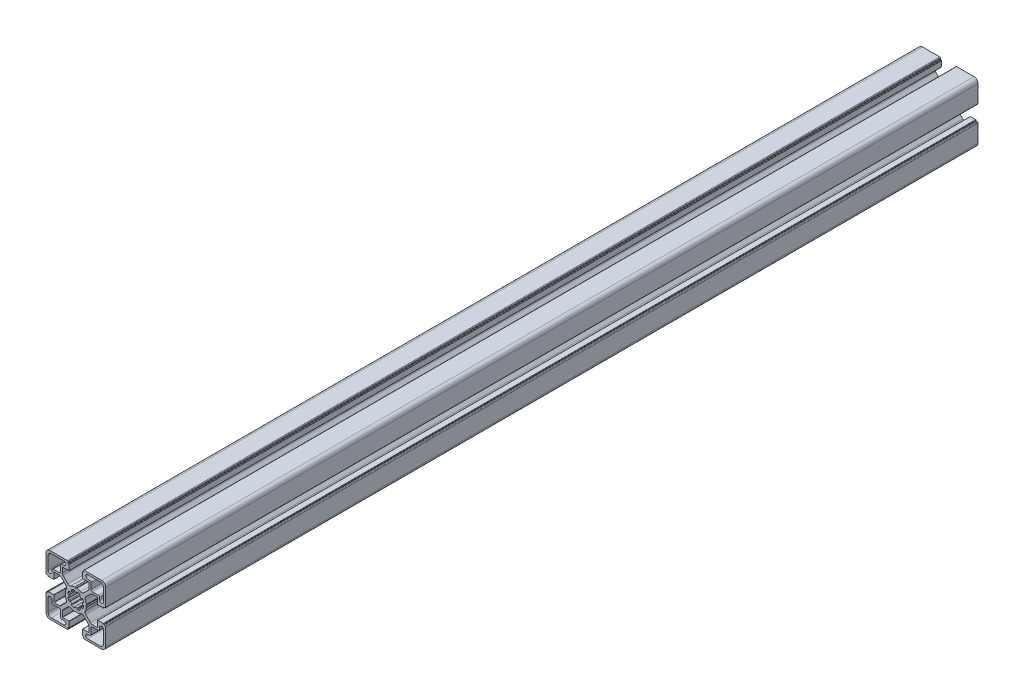
SolidWorks part; units mm, degrees
ref_plane "Front Plane" through (0, 0, 0) normal (0, 0, 1) x (1, 0, 0)
ref_plane "Top Plane" through (0, 0, 0) normal (0, 1, 0) x (1, 0, 0)
ref_plane "Right Plane" through (0, 0, 0) normal (1, 0, 0) x (0, 0, -1)
sketch "Sketch1" plane through (0, 0, 0) normal (0, 0, 1) x (1, 0, 0)
  line L0 (10.55, 18) -> (9, 18)
  line L1 (18.5, 21) -> (9, 21)
  line L2 (21, 9.0002) -> (21, 18.5)
  line L3 (18, 9.0002) -> (18, 10.55)
  line L4 (17, 11.55) -> (12.55, 11.55)
  line L5 (11.55, 12.55) -> (11.55, 17)
  line L6 (7.974, 0.7926) -> (7.5401, 0.0468)
  line L7 (-0.8674, 4.9242) -> (-0.9675, 5.4811)
  line L8 (-3.1913, 4.5626) -> (-2.864, 4.0985)
  line L9 (-4.0897, 2.8765) -> (-4.5668, 3.2082)
  line L10 (-5.4897, 0.9862) -> (-4.9205, 0.8878)
  line L11 (11.1298, 9.425) -> (7.5635, 5.8587)
  line L12 (16.3169, 9.9945) -> (12.5048, 9.9945)
  line L13 (16.5169, 5.2) -> (16.5169, 9.7945)
  line L14 (20.7196, 5) -> (16.7169, 5)
  line L15 (21.0196, 5.3) -> (21.0196, 5.5)
  line L16 (22, 5.8) -> (21.3196, 5.8)
  line L17 (22.5, 6.3) -> (22.5, 19.5)
  line L18 (19.5, 22.5) -> (6.3757, 22.5)
  line L19 (5.8757, 21.3) -> (5.8757, 22)
  line L20 (5.5757, 21) -> (5.3, 21)
  line L21 (5, 16.6668) -> (5, 20.7)
  line L22 (9.9054, 16.4668) -> (5.2, 16.4668)
  line L23 (10.1054, 12.4716) -> (10.1054, 16.2668)
  line L24 (5.9449, 7.4827) -> (9.5196, 11.0574)
  line L25 (0.1126, 7.6069) -> (0.7547, 7.9748)
  line L26 (5.4897, 0.9862) -> (4.9205, 0.8878)
  line L27 (4.0897, 2.8765) -> (4.5668, 3.2082)
  line L28 (3.1913, 4.5626) -> (2.864, 4.0985)
  line L29 (0.8674, 4.9242) -> (0.9675, 5.4811)
  line L30 (-10.55, -18) -> (-9, -18)
  line L31 (-18.5, -21) -> (-9, -21)
  line L32 (-21, -9.0002) -> (-21, -18.5)
  line L33 (-18, -9.0002) -> (-18, -10.55)
  line L34 (-17, -11.55) -> (-12.55, -11.55)
  line L35 (-11.55, -12.55) -> (-11.55, -17)
  line L36 (-7.974, -0.7926) -> (-7.5401, -0.0468)
  line L37 (-11.1298, -9.425) -> (-7.5635, -5.8587)
  line L38 (-16.3169, -9.9945) -> (-12.5048, -9.9945)
  line L39 (-16.5169, -5.2) -> (-16.5169, -9.7945)
  line L40 (-20.7196, -5) -> (-16.7169, -5)
  line L41 (-21.0196, -5.3) -> (-21.0196, -5.5)
  line L42 (-22, -5.8) -> (-21.3196, -5.8)
  line L43 (-22.5, -6.3) -> (-22.5, -19.5)
  line L44 (-19.5, -22.5) -> (-6.3757, -22.5)
  line L45 (-5.8757, -21.3) -> (-5.8757, -22)
  line L46 (-5.5757, -21) -> (-5.3, -21)
  line L47 (-5, -16.6668) -> (-5, -20.7)
  line L48 (-9.9054, -16.4668) -> (-5.2, -16.4668)
  line L49 (-10.1054, -12.4716) -> (-10.1054, -16.2668)
  line L50 (-5.9449, -7.4827) -> (-9.5196, -11.0574)
  line L51 (-0.1126, -7.6069) -> (-0.7547, -7.9748)
  line L52 (0.8674, -4.9242) -> (0.9675, -5.4811)
  line L53 (3.1913, -4.5626) -> (2.864, -4.0985)
  line L54 (4.0897, -2.8765) -> (4.5668, -3.2082)
  line L55 (5.4897, -0.9862) -> (4.9205, -0.8878)
  line L56 (0.1126, -7.6069) -> (0.7547, -7.9748)
  line L57 (5.9449, -7.4827) -> (9.5196, -11.0574)
  line L58 (10.1054, -12.4716) -> (10.1054, -16.2668)
  line L59 (9.9054, -16.4668) -> (5.2, -16.4668)
  line L60 (5, -16.6668) -> (5, -20.7)
  line L61 (5.5757, -21) -> (5.3, -21)
  line L62 (-0.1126, 7.6069) -> (-0.7547, 7.9748)
  line L63 (-5.9449, 7.4827) -> (-9.5196, 11.0574)
  line L64 (-10.1054, 12.4716) -> (-10.1054, 16.2668)
  line L65 (-9.9054, 16.4668) -> (-5.2, 16.4668)
  line L66 (-5, 16.6668) -> (-5, 20.7)
  line L67 (-5.5757, 21) -> (-5.3, 21)
  line L68 (-5.8757, 21.3) -> (-5.8757, 22)
  line L69 (-19.5, 22.5) -> (-6.3757, 22.5)
  line L70 (-22.5, 6.3) -> (-22.5, 19.5)
  line L71 (-22, 5.8) -> (-21.3196, 5.8)
  line L72 (-21.0196, 5.3) -> (-21.0196, 5.5)
  line L73 (-20.7196, 5) -> (-16.7169, 5)
  line L74 (-16.5169, 5.2) -> (-16.5169, 9.7945)
  line L75 (-16.3169, 9.9945) -> (-12.5048, 9.9945)
  line L76 (-11.1298, 9.425) -> (-7.5635, 5.8587)
  line L77 (-7.974, 0.7926) -> (-7.5401, 0.0468)
  line L78 (5.8757, -21.3) -> (5.8757, -22)
  line L79 (19.5, -22.5) -> (6.3757, -22.5)
  line L80 (22.5, -6.3) -> (22.5, -19.5)
  line L81 (22, -5.8) -> (21.3196, -5.8)
  line L82 (21.0196, -5.3) -> (21.0196, -5.5)
  line L83 (20.7196, -5) -> (16.7169, -5)
  line L84 (16.5169, -5.2) -> (16.5169, -9.7945)
  line L85 (16.3169, -9.9945) -> (12.5048, -9.9945)
  line L86 (11.1298, -9.425) -> (7.5635, -5.8587)
  line L87 (-5.4897, -0.9862) -> (-4.9205, -0.8878)
  line L88 (-4.0897, -2.8765) -> (-4.5668, -3.2082)
  line L89 (-3.1913, -4.5626) -> (-2.864, -4.0985)
  line L90 (-0.8674, -4.9242) -> (-0.9675, -5.4811)
  line L91 (7.974, -0.7926) -> (7.5401, -0.0468)
  line L92 (-11.55, 12.55) -> (-11.55, 17)
  line L93 (-17, 11.55) -> (-12.55, 11.55)
  line L94 (-18, 9.0002) -> (-18, 10.55)
  line L95 (-21, 9.0002) -> (-21, 18.5)
  line L96 (-18.5, 21) -> (-9, 21)
  line L97 (-10.55, 18) -> (-9, 18)
  line L98 (11.55, -12.55) -> (11.55, -17)
  line L99 (17, -11.55) -> (12.55, -11.55)
  line L100 (18, -9.0002) -> (18, -10.55)
  line L101 (21, -9.0002) -> (21, -18.5)
  line L102 (18.5, -21) -> (9, -21)
  line L103 (10.55, -18) -> (9, -18)
  line L104 (-33.3633, 0) -> (37.7265, 0) construction
  line L105 (0, 32.2957) -> (0, -36.0465) construction
  arc A0 (9, 18) -> (9, 21) centre (9, 19.5) cw
  arc A1 (18.5, 21) -> (21, 18.5) centre (18.5, 18.5) cw
  arc A2 (21, 9.0002) -> (18, 9.0002) centre (19.5, 9.0002) cw
  arc A3 (17, 11.55) -> (18, 10.55) centre (17, 10.55) cw
  arc A4 (12.55, 11.55) -> (11.55, 12.55) centre (12.55, 12.55) cw
  arc A5 (10.55, 18) -> (11.55, 17) centre (10.55, 17) cw
  arc A6 (7.5313, 0) -> (7.5401, 0.0468) centre (7.7309, -0.013) cw
  arc A7 (8, 0.9141) -> (7.974, 0.7926) centre (7.8011, 0.8932) cw
  arc A8 (7.2004, 3.6119) -> (8, 0.9141) centre (0.0496, 0.0249) cw
  arc A9 (7.2004, 3.6119) -> (7.5635, 5.8587) centre (8.9385, 4.4837) cw
  arc A10 (11.1298, 9.425) -> (12.5048, 9.9945) centre (12.5048, 8.05) cw
  arc A11 (16.3169, 9.9945) -> (16.5169, 9.7945) centre (16.3169, 9.7945) cw
  arc A12 (16.7169, 5) -> (16.5169, 5.2) centre (16.7169, 5.2) cw
  arc A13 (21.0196, 5.3) -> (20.7196, 5) centre (20.7196, 5.3) cw
  arc A14 (0.8674, 4.9242) -> (-0.8674, 4.9242) centre (0, 0) ccw
  arc A15 (-0.9675, 5.4811) -> (-1.5951, 5.8941) centre (-1.4627, 5.4119) ccw
  arc A16 (-1.5951, 5.8941) -> (-3.0444, 5.2994) centre (-0.0235, 0) ccw
  arc A17 (-3.0444, 5.2994) -> (-3.1913, 4.5626) centre (-2.7943, 4.8665) ccw
  arc A18 (-2.864, 4.0985) -> (-4.0897, 2.8765) centre (0, 0) ccw
  arc A19 (-4.5668, 3.2082) -> (-5.3025, 3.0565) centre (-4.868, 2.8091) ccw
  arc A20 (-5.3025, 3.0565) -> (-5.9068, 1.6112) centre (-0.0235, 0) ccw
  arc A21 (-5.9068, 1.6112) -> (-5.4897, 0.9862) centre (-5.4239, 1.4819) ccw
  arc A22 (-4.9205, 0.8878) -> (-5, 0) centre (0, 0) ccw
  arc A23 (21.0196, 5.5) -> (21.3196, 5.8) centre (21.3196, 5.5) cw
  arc A24 (22.5, 6.3) -> (22, 5.8) centre (22, 6.3) cw
  arc A25 (19.5, 22.5) -> (22.5, 19.5) centre (19.5, 19.5) cw
  arc A26 (5.8757, 22) -> (6.3757, 22.5) centre (6.3757, 22) cw
  arc A27 (5.8757, 21.3) -> (5.5757, 21) centre (5.5757, 21.3) cw
  arc A28 (5, 20.7) -> (5.3, 21) centre (5.3, 20.7) cw
  arc A29 (5.2, 16.4668) -> (5, 16.6668) centre (5.2, 16.6668) cw
  arc A30 (9.9054, 16.4668) -> (10.1054, 16.2668) centre (9.9054, 16.2668) cw
  arc A31 (10.1054, 12.4716) -> (9.5196, 11.0574) centre (8.1054, 12.4716) cw
  arc A32 (5.9449, 7.4827) -> (3.6665, 7.1733) centre (4.5855, 8.9496) cw
  arc A33 (0.8764, 8) -> (3.6665, 7.1733) centre (0.0235, 0) cw
  arc A34 (0.7547, 7.9748) -> (0.8764, 8) centre (0.8542, 7.8013) cw
  arc A35 (0.1126, 7.6069) -> (0, 7.531) centre (-0.0489, 7.7249) cw
  arc A36 (4.9205, 0.8878) -> (5, 0) centre (0, 0) cw
  arc A37 (5.9068, 1.6112) -> (5.4897, 0.9862) centre (5.4239, 1.4819) cw
  arc A38 (5.3025, 3.0565) -> (5.9068, 1.6112) centre (0.0235, 0) cw
  arc A39 (4.5668, 3.2082) -> (5.3025, 3.0565) centre (4.868, 2.8091) cw
  arc A40 (2.864, 4.0985) -> (4.0897, 2.8765) centre (0, 0) cw
  arc A41 (3.0444, 5.2994) -> (3.1913, 4.5626) centre (2.7943, 4.8665) cw
  arc A42 (1.5951, 5.8941) -> (3.0444, 5.2994) centre (0.0235, 0) cw
  arc A43 (0.9675, 5.4811) -> (1.5951, 5.8941) centre (1.4627, 5.4119) cw
  arc A44 (-9, -18) -> (-9, -21) centre (-9, -19.5) cw
  arc A45 (-18.5, -21) -> (-21, -18.5) centre (-18.5, -18.5) cw
  arc A46 (-21, -9.0002) -> (-18, -9.0002) centre (-19.5, -9.0002) cw
  arc A47 (-17, -11.55) -> (-18, -10.55) centre (-17, -10.55) cw
  arc A48 (-12.55, -11.55) -> (-11.55, -12.55) centre (-12.55, -12.55) cw
  arc A49 (-10.55, -18) -> (-11.55, -17) centre (-10.55, -17) cw
  arc A50 (-7.5313, 0) -> (-7.5401, -0.0468) centre (-7.7309, 0.013) cw
  arc A51 (-8, -0.9141) -> (-7.974, -0.7926) centre (-7.8011, -0.8932) cw
  arc A52 (-7.2004, -3.6119) -> (-8, -0.9141) centre (-0.0496, -0.0249) cw
  arc A53 (-7.2004, -3.6119) -> (-7.5635, -5.8587) centre (-8.9385, -4.4837) cw
  arc A54 (-11.1298, -9.425) -> (-12.5048, -9.9945) centre (-12.5048, -8.05) cw
  arc A55 (-16.3169, -9.9945) -> (-16.5169, -9.7945) centre (-16.3169, -9.7945) cw
  arc A56 (-16.7169, -5) -> (-16.5169, -5.2) centre (-16.7169, -5.2) cw
  arc A57 (-21.0196, -5.3) -> (-20.7196, -5) centre (-20.7196, -5.3) cw
  arc A58 (-21.0196, -5.5) -> (-21.3196, -5.8) centre (-21.3196, -5.5) cw
  arc A59 (-22.5, -6.3) -> (-22, -5.8) centre (-22, -6.3) cw
  arc A60 (-19.5, -22.5) -> (-22.5, -19.5) centre (-19.5, -19.5) cw
  arc A61 (-5.8757, -22) -> (-6.3757, -22.5) centre (-6.3757, -22) cw
  arc A62 (-5.8757, -21.3) -> (-5.5757, -21) centre (-5.5757, -21.3) cw
  arc A63 (-5, -20.7) -> (-5.3, -21) centre (-5.3, -20.7) cw
  arc A64 (-5.2, -16.4668) -> (-5, -16.6668) centre (-5.2, -16.6668) cw
  arc A65 (-9.9054, -16.4668) -> (-10.1054, -16.2668) centre (-9.9054, -16.2668) cw
  arc A66 (-10.1054, -12.4716) -> (-9.5196, -11.0574) centre (-8.1054, -12.4716) cw
  arc A67 (-5.9449, -7.4827) -> (-3.6665, -7.1733) centre (-4.5855, -8.9496) cw
  arc A68 (-0.8764, -8) -> (-3.6665, -7.1733) centre (-0.0235, 0) cw
  arc A69 (-0.7547, -7.9748) -> (-0.8764, -8) centre (-0.8542, -7.8013) cw
  arc A70 (-0.1126, -7.6069) -> (0, -7.531) centre (0.0489, -7.7249) cw
  arc A71 (0.9675, -5.4811) -> (1.5951, -5.8941) centre (1.4627, -5.4119) ccw
  arc A72 (1.5951, -5.8941) -> (3.0444, -5.2994) centre (0.0235, 0) ccw
  arc A73 (3.0444, -5.2994) -> (3.1913, -4.5626) centre (2.7943, -4.8665) ccw
  arc A74 (2.864, -4.0985) -> (4.0897, -2.8765) centre (0, 0) ccw
  arc A75 (4.5668, -3.2082) -> (5.3025, -3.0565) centre (4.868, -2.8091) ccw
  arc A76 (5.3025, -3.0565) -> (5.9068, -1.6112) centre (0.0235, 0) ccw
  arc A77 (5.9068, -1.6112) -> (5.4897, -0.9862) centre (5.4239, -1.4819) ccw
  arc A78 (4.9205, -0.8878) -> (5, 0) centre (0, 0) ccw
  arc A79 (0.1126, -7.6069) -> (0, -7.531) centre (-0.0489, -7.7249) ccw
  arc A80 (0.7547, -7.9748) -> (0.8764, -8) centre (0.8542, -7.8013) ccw
  arc A81 (0.8764, -8) -> (3.6665, -7.1733) centre (0.0235, 0) ccw
  arc A82 (5.9449, -7.4827) -> (3.6665, -7.1733) centre (4.5855, -8.9496) ccw
  arc A83 (10.1054, -12.4716) -> (9.5196, -11.0574) centre (8.1054, -12.4716) ccw
  arc A84 (9.9054, -16.4668) -> (10.1054, -16.2668) centre (9.9054, -16.2668) ccw
  arc A85 (5.2, -16.4668) -> (5, -16.6668) centre (5.2, -16.6668) ccw
  arc A86 (5, -20.7) -> (5.3, -21) centre (5.3, -20.7) ccw
  arc A87 (5.8757, -21.3) -> (5.5757, -21) centre (5.5757, -21.3) ccw
  arc A88 (-0.1126, 7.6069) -> (0, 7.531) centre (0.0489, 7.7249) ccw
  arc A89 (-0.7547, 7.9748) -> (-0.8764, 8) centre (-0.8542, 7.8013) ccw
  arc A90 (-0.8764, 8) -> (-3.6665, 7.1733) centre (-0.0235, 0) ccw
  arc A91 (-5.9449, 7.4827) -> (-3.6665, 7.1733) centre (-4.5855, 8.9496) ccw
  arc A92 (-10.1054, 12.4716) -> (-9.5196, 11.0574) centre (-8.1054, 12.4716) ccw
  arc A93 (-9.9054, 16.4668) -> (-10.1054, 16.2668) centre (-9.9054, 16.2668) ccw
  arc A94 (-5.2, 16.4668) -> (-5, 16.6668) centre (-5.2, 16.6668) ccw
  arc A95 (-5, 20.7) -> (-5.3, 21) centre (-5.3, 20.7) ccw
  arc A96 (-5.8757, 21.3) -> (-5.5757, 21) centre (-5.5757, 21.3) ccw
  arc A97 (-5.8757, 22) -> (-6.3757, 22.5) centre (-6.3757, 22) ccw
  arc A98 (-19.5, 22.5) -> (-22.5, 19.5) centre (-19.5, 19.5) ccw
  arc A99 (-22.5, 6.3) -> (-22, 5.8) centre (-22, 6.3) ccw
  arc A100 (-21.0196, 5.5) -> (-21.3196, 5.8) centre (-21.3196, 5.5) ccw
  arc A101 (-21.0196, 5.3) -> (-20.7196, 5) centre (-20.7196, 5.3) ccw
  arc A102 (-16.7169, 5) -> (-16.5169, 5.2) centre (-16.7169, 5.2) ccw
  arc A103 (-16.3169, 9.9945) -> (-16.5169, 9.7945) centre (-16.3169, 9.7945) ccw
  arc A104 (-11.1298, 9.425) -> (-12.5048, 9.9945) centre (-12.5048, 8.05) ccw
  arc A105 (-7.2004, 3.6119) -> (-7.5635, 5.8587) centre (-8.9385, 4.4837) ccw
  arc A106 (-7.2004, 3.6119) -> (-8, 0.9141) centre (-0.0496, 0.0249) ccw
  arc A107 (-8, 0.9141) -> (-7.974, 0.7926) centre (-7.8011, 0.8932) ccw
  arc A108 (-7.5313, 0) -> (-7.5401, 0.0468) centre (-7.7309, -0.013) ccw
  arc A109 (5.8757, -22) -> (6.3757, -22.5) centre (6.3757, -22) ccw
  arc A110 (19.5, -22.5) -> (22.5, -19.5) centre (19.5, -19.5) ccw
  arc A111 (22.5, -6.3) -> (22, -5.8) centre (22, -6.3) ccw
  arc A112 (21.0196, -5.5) -> (21.3196, -5.8) centre (21.3196, -5.5) ccw
  arc A113 (-4.9205, -0.8878) -> (-5, 0) centre (0, 0) cw
  arc A114 (-5.9068, -1.6112) -> (-5.4897, -0.9862) centre (-5.4239, -1.4819) cw
  arc A115 (-5.3025, -3.0565) -> (-5.9068, -1.6112) centre (-0.0235, 0) cw
  arc A116 (-4.5668, -3.2082) -> (-5.3025, -3.0565) centre (-4.868, -2.8091) cw
  arc A117 (-2.864, -4.0985) -> (-4.0897, -2.8765) centre (0, 0) cw
  arc A118 (-3.0444, -5.2994) -> (-3.1913, -4.5626) centre (-2.7943, -4.8665) cw
  arc A119 (-1.5951, -5.8941) -> (-3.0444, -5.2994) centre (-0.0235, 0) cw
  arc A120 (-0.9675, -5.4811) -> (-1.5951, -5.8941) centre (-1.4627, -5.4119) cw
  arc A121 (0.8674, -4.9242) -> (-0.8674, -4.9242) centre (0, 0) cw
  arc A122 (21.0196, -5.3) -> (20.7196, -5) centre (20.7196, -5.3) ccw
  arc A123 (16.7169, -5) -> (16.5169, -5.2) centre (16.7169, -5.2) ccw
  arc A124 (-10.55, 18) -> (-11.55, 17) centre (-10.55, 17) ccw
  arc A125 (-12.55, 11.55) -> (-11.55, 12.55) centre (-12.55, 12.55) ccw
  arc A126 (-17, 11.55) -> (-18, 10.55) centre (-17, 10.55) ccw
  arc A127 (-21, 9.0002) -> (-18, 9.0002) centre (-19.5, 9.0002) ccw
  arc A128 (-18.5, 21) -> (-21, 18.5) centre (-18.5, 18.5) ccw
  arc A129 (-9, 18) -> (-9, 21) centre (-9, 19.5) ccw
  arc A130 (16.3169, -9.9945) -> (16.5169, -9.7945) centre (16.3169, -9.7945) ccw
  arc A131 (11.1298, -9.425) -> (12.5048, -9.9945) centre (12.5048, -8.05) ccw
  arc A132 (7.2004, -3.6119) -> (7.5635, -5.8587) centre (8.9385, -4.4837) ccw
  arc A133 (7.2004, -3.6119) -> (8, -0.9141) centre (0.0496, -0.0249) ccw
  arc A134 (8, -0.9141) -> (7.974, -0.7926) centre (7.8011, -0.8932) ccw
  arc A135 (7.5313, 0) -> (7.5401, -0.0468) centre (7.7309, 0.013) ccw
  arc A136 (10.55, -18) -> (11.55, -17) centre (10.55, -17) ccw
  arc A137 (12.55, -11.55) -> (11.55, -12.55) centre (12.55, -12.55) ccw
  arc A138 (17, -11.55) -> (18, -10.55) centre (17, -10.55) ccw
  arc A139 (21, -9.0002) -> (18, -9.0002) centre (19.5, -9.0002) ccw
  arc A140 (18.5, -21) -> (21, -18.5) centre (18.5, -18.5) ccw
  arc A141 (9, -18) -> (9, -21) centre (9, -19.5) ccw
  dimension "D6" = 12.2
  dimension "D8" = 10
  dimension "D1" = 10
  dimension "D2" = 45
  dimension "D3" = 45
  dimension "D4" = 10
  dimension "D5" = 14.5
  dimension "D7" = 22.5
extrude "Base-Extrude" add sketch "Sketch1" against normal blind 659
